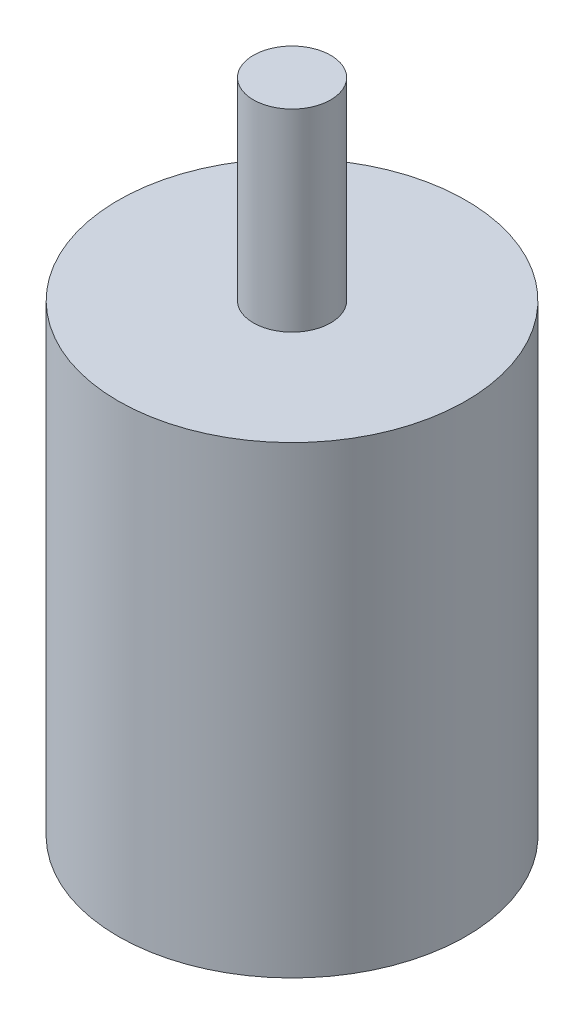
SolidWorks part; units mm, degrees
ref_plane "Front Plane" through (0, 0, 0) normal (0, 0, 1) x (1, 0, 0)
ref_plane "Top Plane" through (0, 0, 0) normal (0, 1, 0) x (1, 0, 0)
ref_plane "Right Plane" through (0, 0, 0) normal (1, 0, 0) x (0, 0, -1)
sketch "Sketch1" plane through (0, 0, 0) normal (0, 1, 0) x (1, 0, 0)
  circle A0 centre (0, 0) radius 22.5
extrude "Boss-Extrude1" add sketch "Sketch1" along normal blind 60
sketch "Sketch2" plane through (0, 60, 0) normal (0, 1, 0) x (1, 0, 0)
  circle A0 centre (0, 0) radius 5
extrude "Boss-Extrude2" add sketch "Sketch2" along normal blind 25
